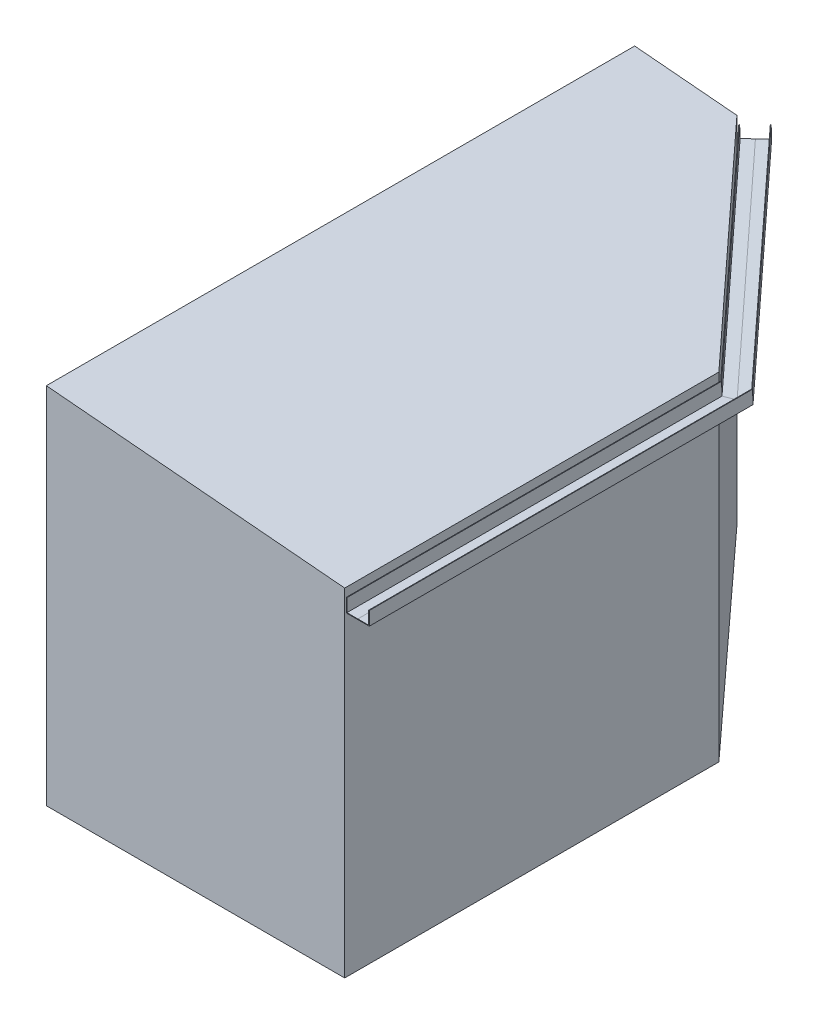
SolidWorks part; units mm, degrees
ref_plane "Ebene vorne" through (0, 0, 0) normal (0, 0, 1) x (1, 0, 0)
ref_plane "Ebene oben" through (0, 0, 0) normal (0, 1, 0) x (1, 0, 0)
ref_plane "Ebene rechts" through (0, 0, 0) normal (1, 0, 0) x (0, 0, -1)
sketch "Skizze1" plane through (0, 0, 0) normal (0, 1, 0) x (1, 0, 0)
  line L3 (-2500, 4930) -> (-2500, 0)
  line L9 (-2500, 0) -> (0, 0)
  line L10 (0, 3135.5476) -> (0, 0)
  line L11 (-2500, 4930) -> (-1643.2248, 4930)
  line L12 (-1643.2248, 4930) -> (0, 3135.5476)
  dimension "D1" = 2500
  dimension "D2" = 4930
  dimension "D3" = 2433.1559
  dimension "D4" = 856.7752
extrude "Aufsatz-Linear austragen1" add sketch "Skizze1" along normal blind 3048.54
sketch "Skizze2" plane through (0, 0, 0) normal (0, 0, 1) x (1, 0, 0)
  line L0 (-2500, 3048.54) -> (0, 2829.8183)
  line L1 (0, 3048.54) -> (0, 0) construction
  line L2 (-2500, 3048.54) -> (0, 3048.54)
  line L3 (0, 3048.54) -> (0, 2829.8183)
  dimension "D1" = 5
extrude "Schnitt-Linear austragen1" cut sketch "Skizze2" against normal through all
sketch "Skizze3" plane through (0, 0, 0) normal (0, 0, 1) x (1, 0, 0)
  line L0 (0, 2829.8183) -> (0, 0) construction
  line L1 (14, 2656) -> (14, 2770)
  line L2 (206, 2770) -> (14, 2770) construction
  line L3 (110, 2770) -> (110, 2656) construction
  line L4 (110, 2656) -> (14, 2656)
  line L5 (-2500, 0) -> (0, 0) construction
  line L6 (19, 2661) -> (19, 2770)
  line L7 (201, 2770) -> (206, 2770)
  line L8 (201, 2661) -> (201, 2770)
  line L9 (206, 2656) -> (206, 2770)
  line L10 (14, 2770) -> (19, 2770)
  line L11 (110, 2656) -> (206, 2656)
  line L12 (110, 2661) -> (19, 2661)
  line L13 (110, 2661) -> (201, 2661)
  line L14 (14, 2656) -> (0, 2656) construction
  dimension "D1" = 182
  dimension "D2" = 192
  dimension "D3" = 114
  dimension "D5" = 110
  dimension "D8" = 5
  dimension "D4" = 91
  dimension "D6" = 2770
  dimension "D7" = 96
ref_plane "Ebene1" through (230.7111, 2637.0402, 0) normal (0.0872, 0.9962, 0) x (0.9962, -0.0872, 0)
sketch "Skizze4" plane through (230.7111, 2637.0402, 0) normal (0.0872, 0.9962, 0) x (0.9962, -0.0872, 0)
  line L0 (-231.5924, 3135.5476) -> (-231.5924, 0)
  line L1 (-231.5924, 3135.5476) -> (-231.5924, 0)
  line L2 (-1881.0941, 4930) -> (-231.5924, 3135.5476)
  line L3 (-1881.0941, 4930) -> (-231.5924, 3135.5476)
sweep "Austragung3" add profiles "Skizze3" path "Skizze4"
